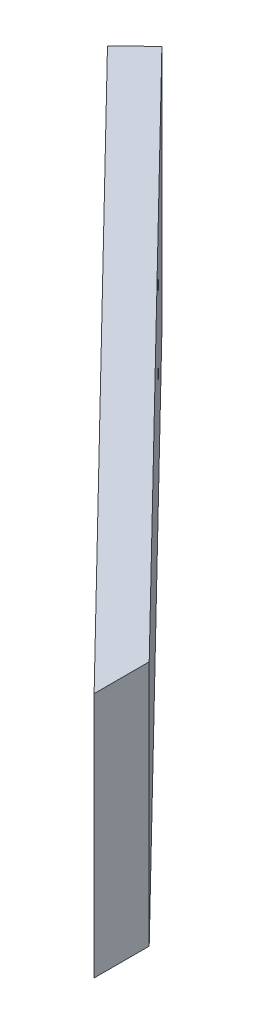
SolidWorks part; units mm, degrees
material "PEI"
ref_plane "Front Plane" through (0, 0, 0) normal (0, 0, 1) x (1, 0, 0)
ref_plane "Top Plane" through (0, 0, 0) normal (0, 1, 0) x (1, 0, 0)
ref_plane "Right Plane" through (0, 0, 0) normal (1, 0, 0) x (0, 0, -1)
sketch "Sketch1" plane through (0, 0, 0) normal (0, 1, 0) x (1, 0, 0)
  line L0 (0, 0) -> (0, 30)
  line L1 (0, 30) -> (83, 115)
  line L2 (0, 0) -> (18.2593, 0) construction
  line L3 (5, 27.9637) -> (5, -27.9637)
  line L5 (5, 27.9637) -> (83, 107.8432)
  line L6 (0, 0) -> (0.2825, 0) construction
  line L7 (5, 1.657) -> (5, 27.9637) construction
  line L8 (83, -115) -> (83, -107.8432)
  line L9 (83, 115) -> (83, 107.8432)
  line L10 (5, 27.9637) -> (86.5774, 111.5068) construction
  line L11 (5, -27.9637) -> (83, -107.8432)
  line L12 (0, -30) -> (83, -115)
  line L13 (0, 0) -> (0, -30)
  line L14 (5, 1.657) -> (5, 1.657) construction
  dimension "D1" = 30
  dimension "D2" = 83
  dimension "D4" = 85
  dimension "D3" = 5
extrude "Boss-Extrude1" add sketch "Sketch1" along normal blind 32
sketch "Sketch2" plane through (0, 32, 0) normal (0, 1, 0) x (1, 0, 0)
  line L0 (83, 115) -> (83, -115)
  line L1 (83, -115) -> (0, -30)
  line L2 (0, -30) -> (0, 30)
  line L3 (0, 30) -> (83, 115)
extrude "Boss-Extrude2" [suppressed] add sketch "Sketch2" along normal blind 5
fillet "Fillet1" radius 10 2 edges at (0, 16, -30) (0, 16, 30)
sketch "Sketch3" [suppressed] plane through (0, 37, 0) normal (0, 1, 0) x (1, 0, 0)
  line L0 (0, 25.9274) -> (0, -25.9274) construction
  line L1 (5, -30) -> (65, -30)
  line L2 (5, -30) -> (5, 30)
  line L3 (5, 30) -> (65, 30)
  line L4 (65, -30) -> (65, 30)
  line L5 (5, -30) -> (65, 30) construction
  line L6 (5, 30) -> (65, -30) construction
  point P0 (35, 0)
  dimension "D1" = 60
  dimension "D2" = 60
  dimension "D3" = 5
extrude "Cut-Extrude1" [suppressed] cut sketch "Sketch3" against normal through all
sketch "Sketch4" plane through (0, 32, 0) normal (0, 1, 0) x (1, 0, 0)
  line L1 (14.5774, -37.7719) -> (86.5774, -111.5068)
  line L4 (120.6904, -133.051) -> (-49.42, -133.051)
  line L6 (14.5774, -37.7719) -> (11, -41.2651)
  line L11 (83, -107.8432) -> (5, -27.9637) construction
  line L12 (2.8453, -32.9138) -> (83, -115) construction
  line L13 (14.5774, 37.7719) -> (11, 41.2651) construction
  line L14 (5, 27.9637) -> (83, 107.8432) construction
  line L15 (83, 115) -> (2.8453, 32.9138) construction
  line L16 (14.5774, -37.7719) -> (14.5774, 37.7719) construction
  line L17 (11, -41.2651) -> (0, -41.2651) construction
  line L18 (0, -41.2651) -> (0, 41.2651) construction
  line L19 (11, 41.2651) -> (0, 41.2651) construction
  line L20 (120.6904, -133.051) -> (120.6904, 124.9571)
  line L21 (120.6904, 124.9571) -> (-49.42, 124.9571)
  line L22 (-49.42, -133.051) -> (-49.42, 124.9571)
  line L23 (86.5774, -111.5068) -> (83, -115)
  line L24 (83, -115) -> (11, -41.2651)
  dimension "D1" = 11
extrude "Cut-Extrude2" cut sketch "Sketch4" against normal through all
sketch "Sketch5" plane through (-11.4184, 0, 11.1497) normal (0.7155, 0, -0.6986) x (-0.6986, 0, -0.7155)
  line L0 (-35.7778, 16) -> (49964.2222, 16) construction
  line L1 (-37.2091, 0) -> (-37.2091, 32) construction
  circle A0 centre (-40.2091, 26) radius 1.1
  circle A1 centre (-40.2091, 6) radius 1.1
  point P6 (-37.2091, 16)
  dimension "D1" = 2.2
  dimension "D2" = 3
  dimension "D3" = 10
extrude "Cut-Extrude3" cut sketch "Sketch5" against normal through all
sketch "Sketch6" plane through (-11.4184, 0, 11.1497) normal (0.7155, 0, -0.6986) x (-0.6986, 0, -0.7155)
  line L0 (-86.1776, 32) -> (-86.1776, -49968) construction
  line L1 (-135.1461, 32) -> (-37.2091, 32) construction
  line L2 (-66.7227, 20) -> (49933.2773, 20) construction
  line L3 (-92.5049, 12) -> (49907.4951, 12) construction
  line L4 (-135.1461, 0) -> (-37.2091, 0) construction
  circle A0 centre (-66.1776, 25) radius 1.1
  circle A1 centre (-66.1776, 15) radius 1.1
  circle A2 centre (-106.1776, 15) radius 1.1
  circle A3 centre (-106.1776, 25) radius 1.1
  circle A4 centre (-86.1776, 17) radius 1.1
  circle A5 centre (-86.1776, 7) radius 1.1
  point P4 (-86.1776, 32)
  dimension "D2" = 2.2
  dimension "D1" = 5
  dimension "D3" = 20
  dimension "D4" = 15
  dimension "D5" = 15
  dimension "D6" = 5
extrude "Cut-Extrude4" cut sketch "Sketch6" against normal through all
